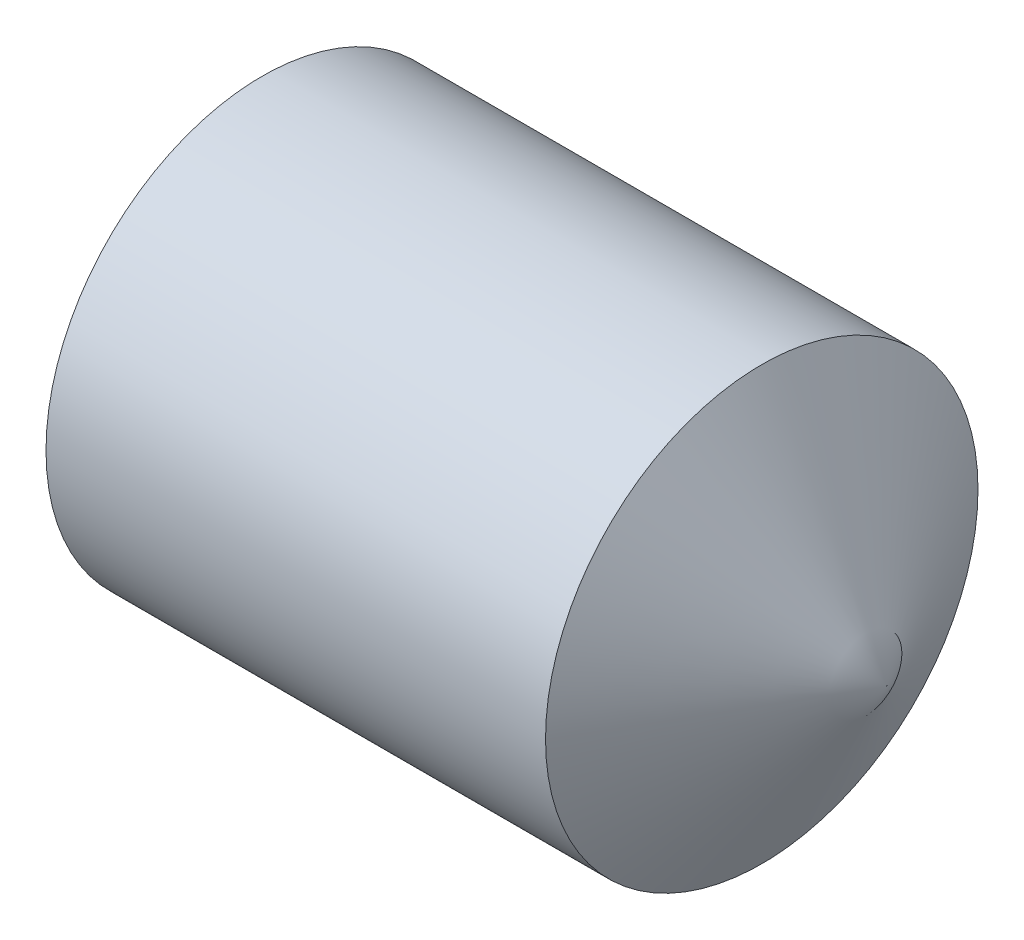
SolidWorks part; units mm, degrees
ref_plane "Plane1" through (0, 0, 0) normal (0, 0, 1) x (1, 0, 0)
ref_plane "Plane2" through (0, 0, 0) normal (0, 1, 0) x (1, 0, 0)
ref_plane "Plane3" through (0, 0, 0) normal (1, 0, 0) x (0, 0, -1)
sketch "BodySke" plane through (0, 0, 0) normal (0, 0, 1) x (1, 0, 0)
  line L0 (0, 0) -> (0, 1.61)
  line L1 (0, 1.61) -> (0.2252, 2)
  line L2 (0.2252, 2) -> (4.8453, 2)
  line L3 (4.8453, 2) -> (6, 0)
  line L4 (6, 0) -> (0, 0)
  line L5 (-12.7, 0) -> (88.9, 0) construction
  line L6 (4.8453, -2) -> (6, 0) construction
  line L7 (0.35, 15.875) -> (0.35, -3.175) construction
  line L8 (0, -1.61) -> (0.2252, -2) construction
  dimension "Cone_ang" = 120
  dimension "Length" = 6
  dimension "Diameter" = 4
  dimension "Drive_ch_ang" = 60
  dimension "Minor_dia" = 3.22
  dimension "Advance" = 0.7
revolve "BaseBody" add sketch "BodySke" angle 360 about L5
cosmetic thread "ThreadCosmetic" [suppressed] parameters "Thread_minor"=3.22
sketch "Sketch2" plane through (0, 0, 0) normal (-1, 0, 0) x (0, 0, 1)
  line L0 (0.5774, 1) -> (-0.5774, 1)
  line L1 (-0.5774, 1) -> (-1.1547, 0)
  line L2 (0.5774, 1) -> (1.1547, 0)
  line L3 (0.5774, -1) -> (1.1547, 0)
  line L4 (0.5774, -1) -> (-0.5774, -1)
  line L5 (-0.5774, -1) -> (-1.1547, 0)
  dimension "Hex_size" = 2
  dimension "D2" = 1
  dimension "D3" = 1
extrude "Hex" cut sketch "Sketch2" against normal blind 1.5
sketch "ThdSchSke" plane through (0, 0, 0) normal (0, 0, 1) x (1, 0, 0)
  line L0 (0.2252, -1.61) -> (-0.0479, -2)
  line L1 (0.2252, -1.61) -> (0.4982, -2)
  line L2 (0.4982, -2) -> (0.4982, -2.5)
  line L3 (-3.175, 0) -> (5.1513, 0) construction
  line L4 (0.2252, 2) -> (0.2252, -2) construction
  line L5 (0.4982, -2.5) -> (-0.0479, -2.5)
  line L6 (-0.0479, -2.5) -> (-0.0479, -2)
  dimension "Thread_minor" = 3.22
  dimension "Diameter" = 4
  dimension "SideAngle" = 55
  dimension "VeeAngle" = 70
  dimension "Overcut" = 5
revolve "ThreadSchematic" [suppressed] cut sketch "ThdSchSke" angle 360 about L3
pattern_linear "ThdSchPat" [suppressed]
equation "\"D2@Sketch2\" = \"Hex_size@Sketch2\" / 2"
equation "\"D3@Sketch2\" = \"Hex_size@Sketch2\" / 2"
equation "\"Thread_minor@ThreadCosmetic\" = \"Minor_dia@BodySke\""
equation "\"Thread_minor@ThdSchSke\" = \"Thread_minor@ThreadCosmetic\""
equation "\"Diameter@ThdSchSke\" = \"Diameter@BodySke\""
equation "\"Overcut@ThdSchSke\" = \"Diameter@BodySke\" * 1.25"
equation "\"Num_threads@ThdSchPat\" = int( (\"Length@BodySke\" - ( ( ( \"Diameter@BodySke\" - \"Minor_dia@BodySke\" ) * 0.5 ) / tan( \"Drive_ch_ang@BodySke\" * 0.017453292 ) ) - ( ( \"Diameter@BodySke\" * 0.5 ) / tan( \"Cone_ang@BodySke\" * 0.008726646 ) ) ) / \"Advance@BodySke\" + 0.999 )  + 1"
equation "\"Advance@ThdSchPat\" = (\"Length@BodySke\" - ( ( ( \"Diameter@BodySke\" - \"Minor_dia@BodySke\" ) * 0.5 ) / tan( \"Drive_ch_ang@BodySke\" * 0.017453292 ) ) - ( ( \"Diameter@BodySke\" * 0.5 ) / tan( \"Cone_ang@BodySke\" * 0.008726646 ) ) ) /  (\"Num_threads@ThdSchPat\" - 1) 'relax it"
equation "' \"Num_threads@ThdSchPat\" = \"Num_threads@ThdSchPat\" - sgn( \"Num_threads@ThdSchPat\" - 1) '---chamfered tips only---"
